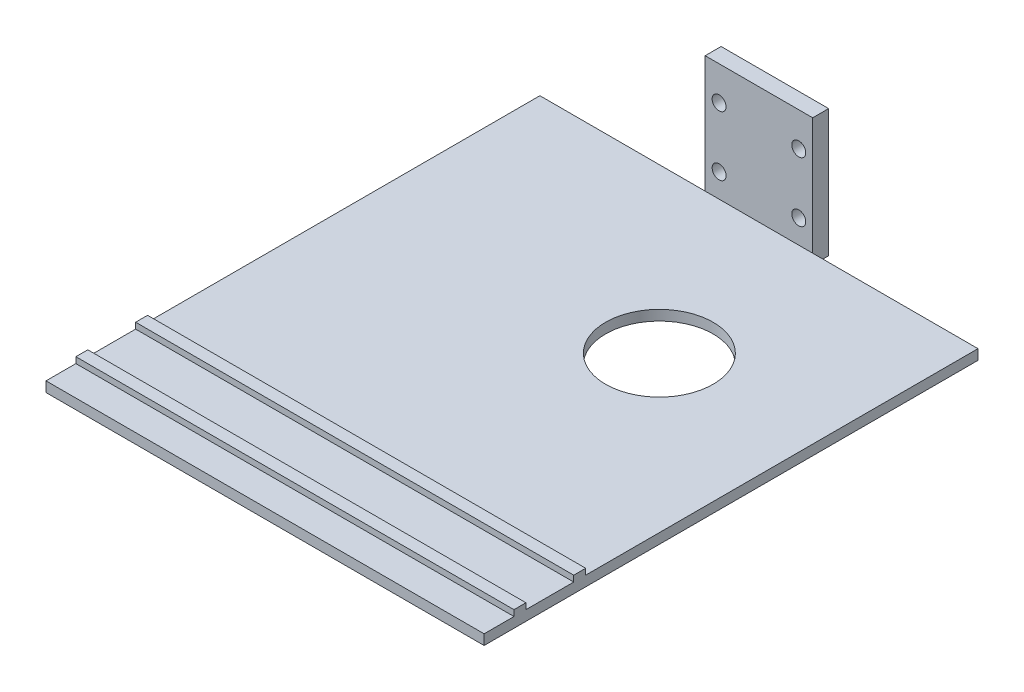
SolidWorks part; units mm, degrees
ref_plane "Piano frontale" through (0, 0, 0) normal (0, 0, 1) x (1, 0, 0)
ref_plane "Piano superiore" through (0, 0, 0) normal (0, 1, 0) x (1, 0, 0)
ref_plane "Piano destro" through (0, 0, 0) normal (1, 0, 0) x (0, 0, -1)
sketch "Schizzo1" plane through (0, 0, 0) normal (0, 0, 1) x (1, 0, 0)
  line L1 (0, 0) -> (27, 0)
  line L2 (0, 0) -> (0, -36)
  line L3 (0, -36) -> (27, -36)
  line L4 (27, 0) -> (27, -36)
  dimension "D1" = 27
  dimension "D2" = 36
extrude "Estrusione-Estrusione1" add sketch "Schizzo1" along normal blind 4
sketch "Schizzo10" plane through (0, 0, 4) normal (0, 0, 1) x (1, 0, 0)
  line L0 (27, 0) -> (0, 0) construction
  line L1 (3.5, -12.5) -> (23.5, -12.5) construction
  line L2 (3.5, -12.5) -> (3.5, -27.5) construction
  line L3 (3.5, -27.5) -> (23.5, -27.5) construction
  line L4 (23.5, -12.5) -> (23.5, -27.5) construction
  line L5 (27, -36) -> (27, 0) construction
  circle A0 centre (3.5, -12.5) radius 1.75
  circle A1 centre (23.5, -12.5) radius 1.75
  circle A2 centre (23.5, -27.5) radius 1.75
  circle A3 centre (3.5, -27.5) radius 1.75
  dimension "D5" = 3.5
  dimension "D1" = 12.5
  dimension "D2" = 15
  dimension "D3" = 20
  dimension "D4" = 3.5
extrude "Taglio-Estrusione5" cut sketch "Schizzo10" against normal blind 10
ref_plane "Piano1" through (13.5, 0, 0) normal (1, 0, 0) x (0, 0, -1)
sketch "Schizzo12" plane through (13.5, 0, 0) normal (1, 0, 0) x (0, 0, -1)
  line L1 (-4, -36) -> (-128, -36)
  line L2 (-4, -36) -> (-4, -33.4507)
  line L3 (-4, -33.4507) -> (-128, -33.4507)
  line L4 (-128, -36) -> (-128, -33.4507)
  dimension "D1" = 124
extrude "Estrusione-Estrusione2" add sketch "Schizzo12" along normal blind 55 and the other way blind 55
sketch "Schizzo14" plane through (-41.5, 0, 0) normal (-1, 0, 0) x (0, 0, 1)
  line L0 (4, -33.4507) -> (128, -33.4507) construction
  line L1 (102.5, -33.4507) -> (105.5, -33.4507)
  line L2 (102.5, -33.4507) -> (102.5, -31.9507)
  line L3 (102.5, -31.9507) -> (105.5, -31.9507)
  line L4 (105.5, -33.4507) -> (105.5, -31.9507)
  line L5 (128, -33.4507) -> (128, -36) construction
  line L6 (117.5, -33.4507) -> (120.5, -33.4507)
  line L7 (117.5, -33.4507) -> (117.5, -31.9507)
  line L8 (117.5, -31.9507) -> (120.5, -31.9507)
  line L9 (120.5, -33.4507) -> (120.5, -31.9507)
  dimension "D1" = 7.5
  dimension "D2" = 12
  dimension "D3" = 1.5
  dimension "D4" = 3
extrude "Estrusione-Estrusione3" add sketch "Schizzo14" against normal blind 110
sketch "Schizzo15" plane through (0, 0, 4) normal (0, 0, 1) x (1, 0, 0)
  line L0 (27, -33.4507) -> (27, 0) construction
  line L1 (0, 0) -> (27, 0)
  line L2 (0, 0) -> (0, -4)
  line L3 (0, -4) -> (27, -4)
  line L4 (27, 0) -> (27, -4)
  dimension "D1" = 4
extrude "Taglio-Estrusione6" cut sketch "Schizzo15" against normal through all
sketch "Schizzo16" plane through (0, -33.4507, 0) normal (0, 1, 0) x (1, 0, 0)
  line L0 (68.5, -45) -> (29.5, -45) construction
  line L1 (68.5, -4) -> (68.5, -102.5) construction
  line L2 (29.5, -4) -> (29.5, -45) construction
  line L3 (27, -4) -> (68.5, -4) construction
  circle A0 centre (29.5, -45) radius 13.5
  dimension "D3" = 27
  dimension "D1" = 39
  dimension "D2" = 41
extrude "Taglio-Estrusione7" cut sketch "Schizzo16" against normal blind 10
